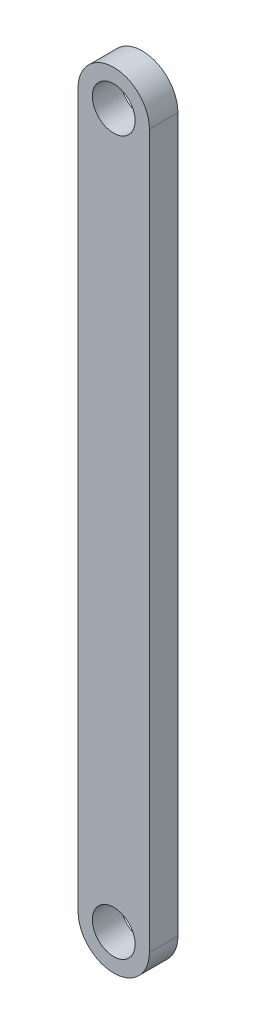
SolidWorks part; units mm, degrees
material "CA"
ref_plane "Ön Düzlem" through (0, 0, 0) normal (0, 0, 1) x (1, 0, 0)
ref_plane "Üst Düzlem" through (0, 0, 0) normal (0, 1, 0) x (1, 0, 0)
ref_plane "Sağ Düzlem" through (0, 0, 0) normal (1, 0, 0) x (0, 0, -1)
sketch "Çizim1" plane through (0, 0, 0) normal (0, 0, 1) x (1, 0, 0)
  line L0 (0, 0) -> (0, 50) construction
  line L1 (-2.5, 0) -> (-2.5, 50)
  line L2 (2.5, 50) -> (2.5, 0)
  circle A0 centre (0, 0) radius 2.5
  circle A1 centre (0, 50) radius 2.5
  dimension "D1" = 5
  dimension "D3" = 5
  dimension "D2" = 50
extrude "Yükseklik-Ekstrüzyon1" add sketch "Çizim1" against normal blind 2
sketch "Çizim3" plane through (0, 0, 0) normal (0, 0, 1) x (1, 0, 0)
  circle A0 centre (0, 0) radius 1.5
  dimension "D1" = 3
extrude "Kes-Ekstrüzyon1" cut sketch "Çizim3" against normal through all
ref_point "Nokta1"
sketch "Çizim5" plane through (0, 0, 0) normal (0, 0, 1) x (1, 0, 0)
  circle A0 centre (0, 50) radius 1.5
  dimension "D1" = 3
extrude "Kes-Ekstrüzyon2" cut sketch "Çizim5" against normal blind 2
